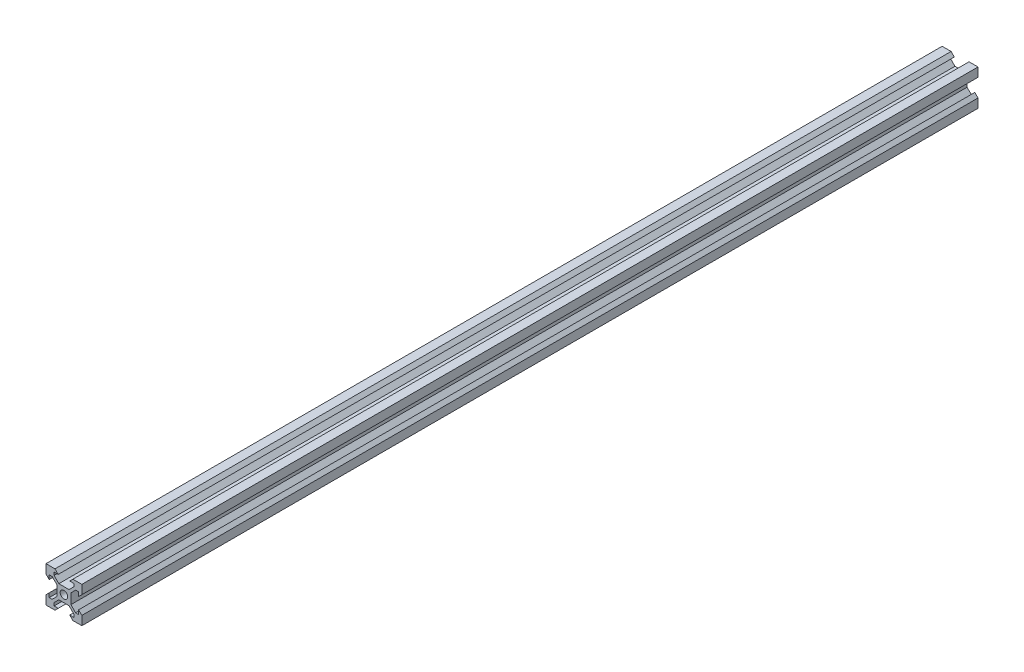
SolidWorks part; units mm, degrees
material "6063-T5"
ref_plane "Front Plane" through (0, 0, 0) normal (0, 0, 1) x (1, 0, 0)
ref_plane "Top Plane" through (0, 0, 0) normal (0, 1, 0) x (1, 0, 0)
ref_plane "Right Plane" through (0, 0, 0) normal (1, 0, 0) x (0, 0, -1)
sketch "Sketch1" plane through (0, 0, 0) normal (0, 0, 1) x (1, 0, 0)
  line L0 (-10, 10) -> (-5, 10)
  line L1 (10, -10) -> (-10, -10) construction
  line L2 (10, -10) -> (10, 10) construction
  line L3 (10, 10) -> (-10, 10) construction
  line L4 (-10, -10) -> (-10, 10) construction
  line L5 (10, -10) -> (-10, 10) construction
  line L6 (10, 10) -> (-10, -10) construction
  line L7 (-5, 10) -> (-3.2, 8.2)
  line L8 (-3.2, 8.2) -> (-5.4993, 8.2)
  line L9 (-5.4993, 8.2) -> (-5.4993, 6.56)
  line L10 (-2.84, 3.9007) -> (2.84, 3.9007)
  line L11 (0, 3.9007) -> (0, 2.1) construction
  line L12 (-5.4993, 6.56) -> (-2.84, 3.9007)
  line L13 (0, 0) -> (0, -13.2939) construction
  line L14 (0, 0) -> (-17.0802, 0) construction
  line L15 (-10, 10) -> (-10, 5)
  line L16 (-10, 5) -> (-8.2, 3.2)
  line L17 (-8.2, 3.2) -> (-8.2, 5.4993)
  line L18 (-8.2, 5.4993) -> (-6.56, 5.4993)
  line L19 (-6.56, 5.4993) -> (-3.9007, 2.84)
  line L20 (-3.9007, 2.84) -> (-3.9007, -2.84)
  line L21 (-3.2, -8.2) -> (-5.4993, -8.2)
  line L22 (-5.4993, -8.2) -> (-5.4993, -6.56)
  line L23 (-5, -10) -> (-3.2, -8.2)
  line L24 (-10, -10) -> (-5, -10)
  line L25 (-10, -10) -> (-10, -5)
  line L26 (-10, -5) -> (-8.2, -3.2)
  line L27 (-8.2, -3.2) -> (-8.2, -5.4993)
  line L28 (-8.2, -5.4993) -> (-6.56, -5.4993)
  line L29 (-6.56, -5.4993) -> (-3.9007, -2.84)
  line L30 (-5.4993, -6.56) -> (-2.84, -3.9007)
  line L31 (-2.84, -3.9007) -> (2.84, -3.9007)
  line L32 (5.4993, 6.56) -> (2.84, 3.9007)
  line L33 (3.2, 8.2) -> (5.4993, 8.2)
  line L34 (5.4993, 8.2) -> (5.4993, 6.56)
  line L35 (5, 10) -> (3.2, 8.2)
  line L36 (10, 10) -> (5, 10)
  line L37 (10, 10) -> (10, 5)
  line L38 (10, 5) -> (8.2, 3.2)
  line L39 (8.2, 3.2) -> (8.2, 5.4993)
  line L40 (8.2, 5.4993) -> (6.56, 5.4993)
  line L41 (6.56, 5.4993) -> (3.9007, 2.84)
  line L42 (3.9007, 2.84) -> (3.9007, -2.84)
  line L43 (6.56, -5.4993) -> (3.9007, -2.84)
  line L44 (8.2, -5.4993) -> (6.56, -5.4993)
  line L45 (8.2, -3.2) -> (8.2, -5.4993)
  line L46 (10, -5) -> (8.2, -3.2)
  line L47 (10, -10) -> (10, -5)
  line L48 (10, -10) -> (5, -10)
  line L49 (5, -10) -> (3.2, -8.2)
  line L50 (3.2, -8.2) -> (5.4993, -8.2)
  line L51 (5.4993, -8.2) -> (5.4993, -6.56)
  line L52 (5.4993, -6.56) -> (2.84, -3.9007)
  circle A0 centre (0, 0) radius 2.1
  arc A1 (0, -2.1) -> (0, 2.1) centre (0, 0) cw construction
  point P0 (0, 0)
  point P25 (-3.9007, 0)
  point P35 (0, 0)
  point P56 (0, -3.9007)
  dimension "D2" = 4.2
  dimension "D1" = 20
  dimension "D3" = 1.64
  dimension "D4" = 1.8
  dimension "D5" = 45
  dimension "D6" = 1.5
  dimension "D7" = 5.68
  dimension "D8" = 5
extrude "Boss-Extrude1" add sketch "Sketch1" along normal mid plane 500
